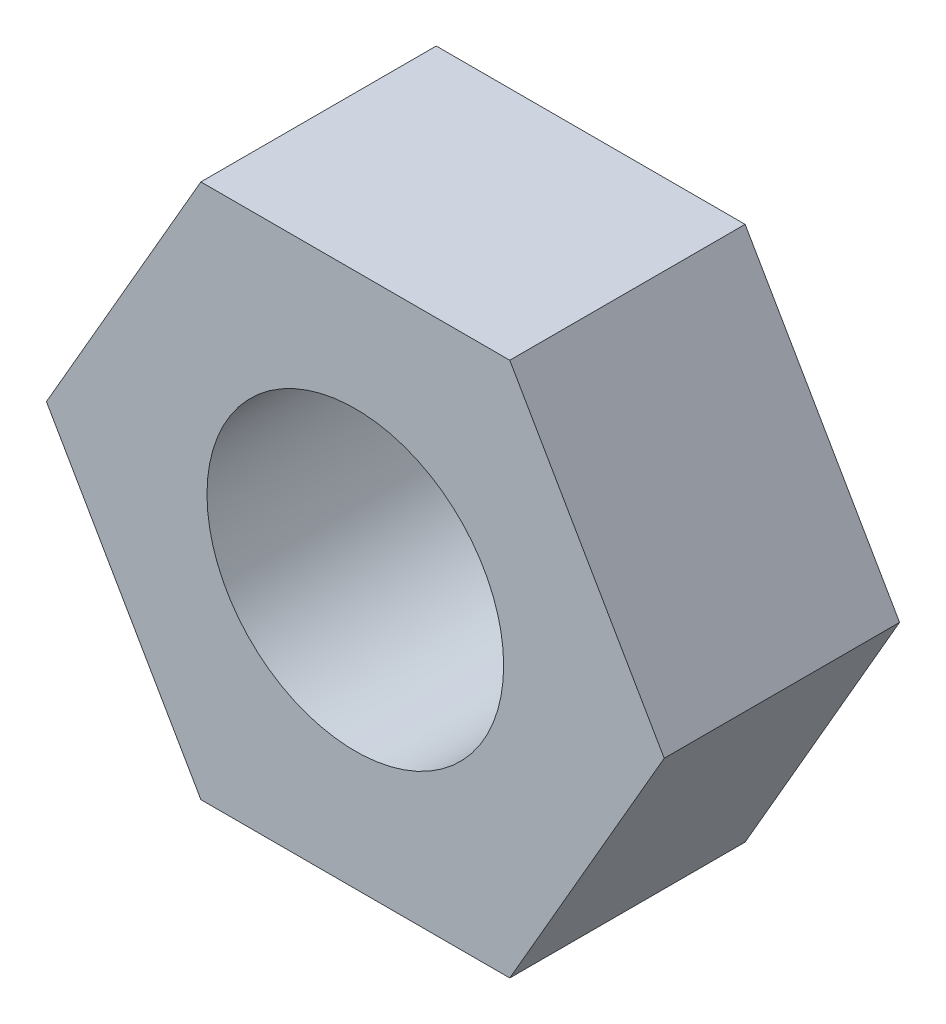
SolidWorks part; units mm, degrees
material "201 Annealed Stainless Steel (SS)"
ref_plane "Front Plane" through (0, 0, 0) normal (0, 0, 1) x (1, 0, 0)
ref_plane "Top Plane" through (0, 0, 0) normal (0, 1, 0) x (1, 0, 0)
ref_plane "Right Plane" through (0, 0, 0) normal (1, 0, 0) x (0, 0, -1)
sketch "Sketch1" plane through (0, 0, 0) normal (0, 0, 1) x (1, 0, 0)
  line L1 (1.5617, -2.705) -> (3.1235, 0)
  line L2 (3.1235, 0) -> (1.5617, 2.705)
  line L3 (1.5617, 2.705) -> (-1.5617, 2.705)
  line L4 (-1.5617, 2.705) -> (-3.1235, 0)
  line L5 (-3.1235, 0) -> (-1.5617, -2.705)
  line L6 (-1.5617, -2.705) -> (1.5617, -2.705)
  circle A0 centre (0, 0) radius 2.705 construction
  circle A1 centre (0, 0) radius 1.5
  dimension "D2" = 3
  dimension "D1" = 5.41
extrude "Boss-Extrude1" add sketch "Sketch1" along normal blind 2.38
